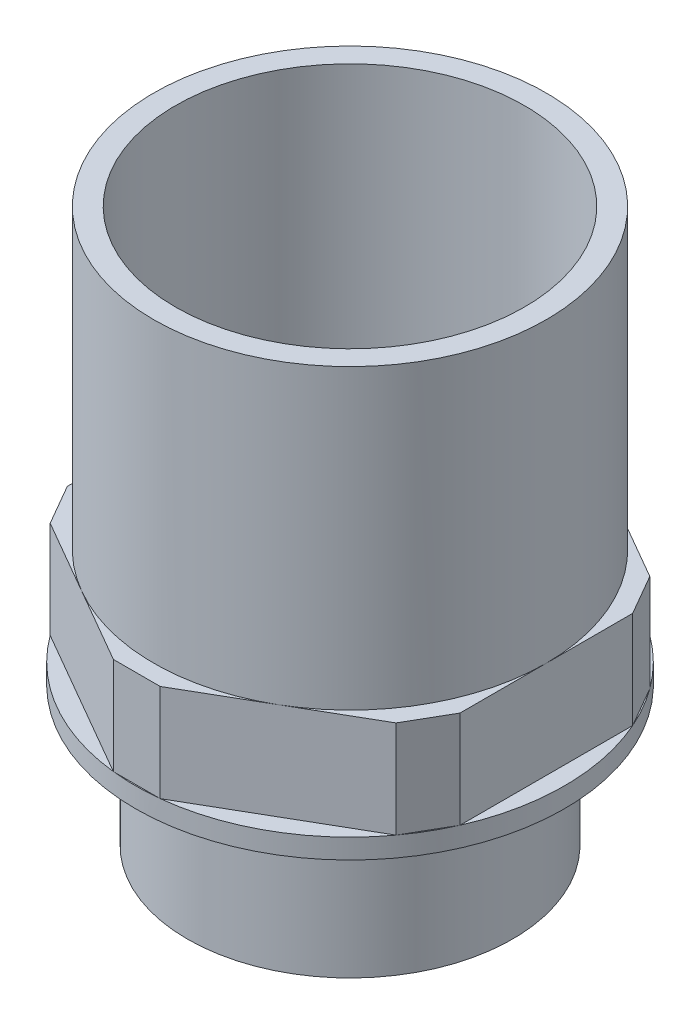
SolidWorks part; units mm, degrees
ref_plane "PRT Front" through (0, 0, 0) normal (0, 0, 1) x (1, 0, 0)
ref_plane "PRT Top" through (0, 0, 0) normal (0, 1, 0) x (1, 0, 0)
ref_plane "PRT Side" through (0, 0, 0) normal (1, 0, 0) x (0, 0, -1)
sketch "Sketch2" plane through (0, 0, 0) normal (0, 1, 0) x (1, 0, 0)
  circle A0 centre (0, 0) radius 20.828
  dimension "D1" = 41.656
extrude "Base-Extrude" add sketch "Sketch2" along normal blind 17.78
sketch "Sketch3" plane through (0, 17.78, 0) normal (0, 1, 0) x (-1, 0, 0)
  circle A0 centre (0, 0) radius 27.4701
  dimension "D1" = 54.9402
extrude "Boss-Extrude1" add sketch "Sketch3" along normal blind 2.54
sketch "Sketch5" plane through (0, 20.32, 0) normal (0, 1, 0) x (-1, 0, 0)
  line L0 (25.146, -11.0583) -> (25.146, 11.0583)
  line L1 (-25.146, -11.0583) -> (-25.146, 11.0583)
  line L2 (0, 0) -> (0, 9.7914) construction
  line L3 (22.1497, 16.2479) -> (2.9963, 27.3062)
  line L4 (-2.9963, -27.3062) -> (-22.1497, -16.2479)
  line L5 (0, 0) -> (-9.5741, 5.5276) construction
  line L6 (-22.1497, 16.2479) -> (-2.9963, 27.3062)
  line L7 (2.9963, -27.3062) -> (22.1497, -16.2479)
  line L8 (0, 0) -> (-9.9628, -5.752) construction
  line L9 (25.146, 11.0583) -> (22.1497, 16.2479)
  line L10 (2.9963, 27.3062) -> (-2.9963, 27.3062)
  line L11 (25.146, -11.0583) -> (22.1497, -16.2479)
  line L12 (2.9963, -27.3062) -> (-2.9963, -27.3062)
  line L13 (-22.1497, -16.2479) -> (-25.146, -11.0583)
  line L14 (-22.1497, 16.2479) -> (-25.146, 11.0583)
  circle A0 centre (0, 0) radius 27.4701 construction
  dimension "D1" = 50.292
  dimension "D2" = 60
  dimension "D3" = 50.292
  dimension "D4" = 60
  dimension "D5" = 50.292
extrude "Boss-Extrude3" add sketch "Sketch5" along normal blind 12.446
sketch "Sketch6" plane through (0, 32.766, 0) normal (0, 1, 0) x (-1, 0, 0)
  circle A0 centre (0, 0) radius 25.146
extrude "Boss-Extrude4" add sketch "Sketch6" along normal blind 38.1
sketch "Sketch7" plane through (0, 70.866, 0) normal (0, 1, 0) x (-1, 0, 0)
  circle A0 centre (0, 0) radius 22.352
  dimension "D1" = 44.704
extrude "Cut-Extrude1" cut sketch "Sketch7" against normal blind 50.546
sketch "Sketch8" plane through (0, 0, 0) normal (0, -1, 0) x (1, 0, 0)
  circle A0 centre (0, 0) radius 17.145
  dimension "D1" = 34.29
extrude "Cut-Extrude2" cut sketch "Sketch8" against normal through all
